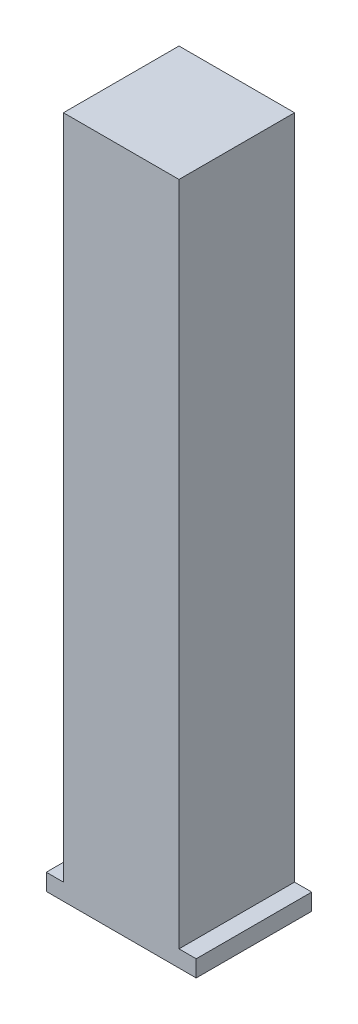
SolidWorks part; units mm, degrees
ref_plane "Front Plane" through (0, 0, 0) normal (0, 0, 1) x (1, 0, 0)
ref_plane "Top Plane" through (0, 0, 0) normal (0, 1, 0) x (1, 0, 0)
ref_plane "Right Plane" through (0, 0, 0) normal (1, 0, 0) x (0, 0, -1)
sketch "Sketch1" plane through (0, 0, 0) normal (0, 1, 0) x (1, 0, 0)
  line L1 (-14.2875, 11.0125) -> (14.2875, 11.0125)
  line L2 (-14.2875, 11.0125) -> (-14.2875, -11.0125)
  line L3 (-14.2875, -11.0125) -> (14.2875, -11.0125)
  line L4 (14.2875, 11.0125) -> (14.2875, -11.0125)
  line L5 (-14.2875, 11.0125) -> (14.2875, -11.0125) construction
  line L6 (-14.2875, -11.0125) -> (14.2875, 11.0125) construction
  point P0 (0, 0)
  dimension "D1" = 22.025
  dimension "D2" = 28.575
extrude "Boss-Extrude1" add sketch "Sketch1" along normal blind 3.175
sketch "Sketch2" plane through (0, 3.175, 0) normal (0, 1, 0) x (1, 0, 0)
  line L1 (-11.0125, 11.0125) -> (11.0125, 11.0125)
  line L2 (-11.0125, 11.0125) -> (-11.0125, -11.0125)
  line L3 (-11.0125, -11.0125) -> (11.0125, -11.0125)
  line L4 (11.0125, 11.0125) -> (11.0125, -11.0125)
  line L5 (-11.0125, 11.0125) -> (11.0125, -11.0125) construction
  line L6 (-11.0125, -11.0125) -> (11.0125, 11.0125) construction
  point P0 (0, 0)
  dimension "D1" = 22.025
  dimension "D2" = 22.025
extrude "Boss-Extrude2" add sketch "Sketch2" along normal blind 127
